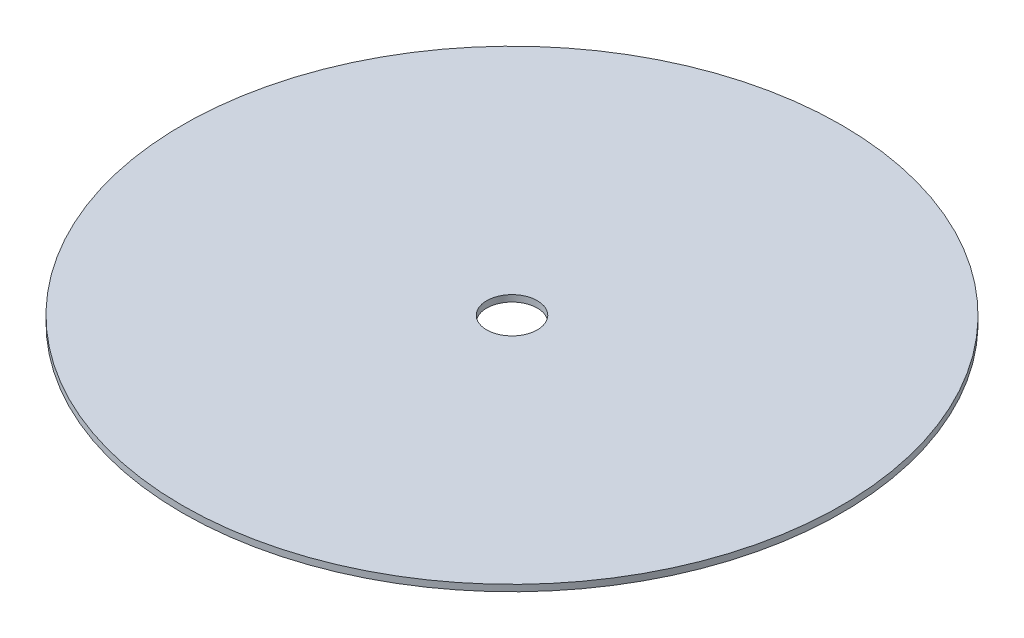
SolidWorks part; units mm, degrees
ref_plane "Front Plane" through (0, 0, 0) normal (0, 0, 1) x (1, 0, 0)
ref_plane "Top Plane" through (0, 0, 0) normal (0, 1, 0) x (1, 0, 0)
ref_plane "Right Plane" through (0, 0, 0) normal (1, 0, 0) x (0, 0, -1)
sketch "Sketch2" plane through (0, 0, 0) normal (0, 1, 0) x (1, 0, 0)
  circle A0 centre (0, 0) radius 153
  circle A1 centre (0, 0) radius 11.75
  point P4 (0, 0)
  point P5 (0, 0)
  dimension "D1" = 306
  dimension "D2" = 23.5
extrude "Boss-Extrude1" add sketch "Sketch2" along normal blind 3
